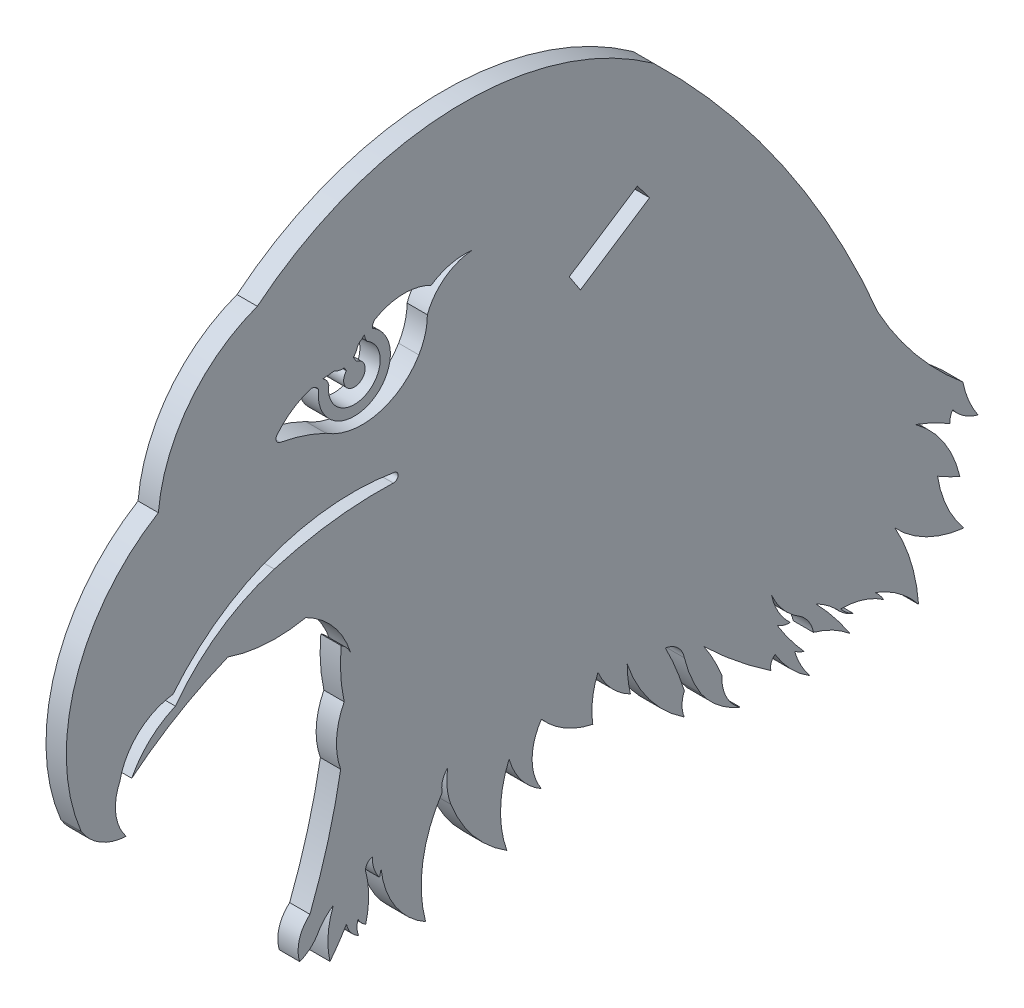
SolidWorks part; units mm, degrees
ref_plane "Front Plane" through (0, 0, 0) normal (0, 0, 1) x (1, 0, 0)
ref_plane "Top Plane" through (0, 0, 0) normal (0, 1, 0) x (1, 0, 0)
ref_plane "Right Plane" through (0, 0, 0) normal (1, 0, 0) x (0, 0, -1)
sketch "Sketch1" plane through (0, 0, 0) normal (1, 0, 0) x (0, 0, -1)
  line L0 (-5.157, -1.535) -> (-5.157, 113.227) construction
  line L1 (-57.5068, 40.0093) -> (-57.736, 40.3716)
  line L2 (-58.2534, 39.7641) -> (-58.4265, 40.0378)
  line L3 (-40.6972, 36.2408) -> (-41.5304, 37.5169)
  line L4 (-41.5304, 37.5169) -> (-36.4188, 40.8543)
  line L6 (-36.4188, 40.8543) -> (-35.4983, 39.6353)
  line L8 (-35.4983, 39.6353) -> (-40.6972, 36.2408)
  arc A102 (-56.508, 41.2313) -> (-59.9592, 39.5319) centre (-57.66, 39.2166) cw construction
  arc A103 (-39.7661, 7.5382) -> (-39.3767, 10.7275) centre (-33.821, 8.4307) cw
  arc A104 (-43.6183, 9.7965) -> (-39.7661, 7.5382) centre (-38.3341, 14.3956) ccw
  arc A105 (-43.6183, 5.2799) -> (-43.6183, 9.7965) centre (-40.3275, 7.5382) cw
  arc A106 (-46.0451, 8.4226) -> (-43.6183, 5.2799) centre (-41.0176, 9.7965) ccw
  arc A107 (-46.2125, 2.5605) -> (-46.0451, 8.4226) centre (-38.7171, 5.2799) cw
  arc A108 (-50.4104, 7.6526) -> (-46.2125, 2.5605) centre (-40.7067, 11.3758) ccw
  arc A109 (-50.6521, 10.1597) -> (-50.4104, 7.6526) centre (-46.0063, 9.3425) ccw
  arc A110 (-51.0669, 8.7672) -> (-50.6521, 10.1597) centre (-49.6143, 9.0925) cw
  arc A111 (-36.9389, 8.0929) -> (-39.3767, 10.7275) centre (-34.4893, 12.8046) cw
  arc A112 (-37.181, 10.1597) -> (-36.9389, 8.0929) centre (-27.6651, 10.2266) ccw
  arc A113 (-32.8896, 4.5676) -> (-37.181, 10.1597) centre (-26.8849, 13.6183) cw
  arc A114 (-32.8896, 6.2719) -> (-32.8896, 4.5676) centre (-30.947, 5.4198) ccw
  arc A115 (-34.3147, 9.774) -> (-32.8896, 6.2719) centre (-53.5231, -0.0839) cw
  arc A116 (-32.8896, 8.4226) -> (-34.3147, 9.774) centre (-34.5555, 8.0929) ccw
  arc A117 (-31.6349, 5.4546) -> (-32.8896, 8.4226) centre (-23.0512, 10.8322) cw
  arc A118 (-28.6904, 3.1113) -> (-31.6349, 5.4546) centre (-26.2232, 9.2331) cw
  arc A119 (-30.0731, 5.8899) -> (-28.6904, 3.1113) centre (-26.941, 5.7151) ccw
  arc A120 (-31.423, 8.4226) -> (-30.0731, 5.8899) centre (-43.6183, 0.2968) cw
  arc A121 (-26.3889, 4.3396) -> (-31.423, 8.4226) centre (-5.4221, 35.3348) cw
  arc A122 (-26.0773, 5.2334) -> (-26.3889, 4.3396) centre (-25.6051, 4.5676) ccw
  arc A123 (-52.3123, 0.9777) -> (-51.0669, 8.7672) centre (-42.9916, 3.4818) cw
  arc A124 (-55.6544, 6.0835) -> (-52.3123, 0.9777) centre (-48.9859, 6.8018) ccw
  arc A125 (-55.763, 5.581) -> (-55.6544, 6.0835) centre (-52.1689, 5.0674) cw
  arc A126 (-56.3189, 7.195) -> (-55.763, 5.581) centre (-53.8194, 7.1531) ccw
  arc A127 (-56.8126, 6.5016) -> (-56.3189, 7.195) centre (-56.1989, 6.5871) cw
  arc A128 (-56.8126, 3.058) -> (-56.8126, 6.5016) centre (-63.2666, 4.7798) ccw
  arc A129 (-57.3883, 3.6721) -> (-56.8126, 3.058) centre (-56.0238, 4.3743) ccw
  arc A130 (-57.3325, 2.5959) -> (-57.3883, 3.6721) centre (-55.9912, 3.2049) cw
  arc A131 (-58.2536, 3.7943) -> (-57.3325, 2.5959) centre (-56.5677, 4.1369) ccw
  arc A132 (-23.4374, 2.5249) -> (-26.0773, 5.2334) centre (-19.2612, 9.236) cw
  arc A133 (-24.6137, 4.703) -> (-23.4374, 2.5249) centre (-18.8822, 6.3917) ccw
  arc A134 (-23.9034, 4.3396) -> (-24.6137, 4.703) centre (-23.0333, 6.9168) cw
  arc A135 (-25.9299, 7.0524) -> (-23.9034, 4.3396) centre (-9.2236, 17.4195) ccw
  arc A136 (-24.9371, 6.7473) -> (-25.9299, 7.0524) centre (-24.9656, 8.4226) cw
  arc A137 (-26.3438, 9.2205) -> (-24.9371, 6.7473) centre (-21.8152, 10.1597) ccw
  arc A138 (-24.1654, 6.7473) -> (-26.3438, 9.2205) centre (-21.4141, 11.3667) cw
  arc A139 (-23.2036, 5.2334) -> (-24.1654, 6.7473) centre (-25.5653, 4.7954) ccw
  arc A140 (-20.4638, 3.7943) -> (-23.2036, 5.2334) centre (-25.2319, -1.9557) ccw
  arc A141 (-23.0216, 6.9921) -> (-20.4638, 3.7943) centre (-38.3705, -7.9066) cw
  arc A142 (-21.4881, 5.8899) -> (-23.0216, 6.9921) centre (-25.7182, 1.6227) ccw
  arc A143 (-20.2087, 4.9703) -> (-21.4881, 5.8899) centre (-19.0523, 7.9289) cw
  arc A144 (-21.1717, 5.7376) -> (-20.2087, 4.9703) centre (-18.895, 7.6071) ccw
  arc A145 (-17.9051, 4.7108) -> (-21.1717, 5.7376) centre (-21.1516, 0.0918) ccw
  arc A146 (-17.9051, 4.7108) -> (-18.5639, 5.5084) centre (-21.4104, 2.4864) ccw
  arc A147 (-15.3111, 3.1113) -> (-18.5639, 5.5084) centre (-21.2448, -1.535) ccw
  arc A148 (-17.0835, 8.9562) -> (-15.3111, 3.1113) centre (-29.2416, 2.0782) cw
  arc A149 (-11.9046, 6.3713) -> (-17.0835, 8.9562) centre (-10.9858, 14.6927) cw
  arc A150 (-13.8837, 10.7275) -> (-11.9046, 6.3713) centre (-5.157, 12.0646) ccw
  arc A151 (-12.2144, 9.8825) -> (-13.8837, 10.7275) centre (-6.9373, 22.3791) cw
  arc A152 (-15.5359, 14.9115) -> (-12.2144, 9.8825) centre (-20.5903, 7.9618) cw
  arc A153 (-59.4908, 1.9849) -> (-58.2536, 3.7943) centre (-71.3915, 11.4489) ccw
  arc A154 (-74.3728, 21.3352) -> (-67.1612, 25.6056) centre (-56.0439, -1.3932) cw
  arc A155 (-71.0947, 24.3852) -> (-74.3728, 21.3352) centre (-68.5194, 18.3306) ccw
  arc A156 (-63.6766, 29.5837) -> (-71.0947, 24.3852) centre (-59.654, 15.9518) ccw
  arc A157 (-54.7401, 30.7082) -> (-63.6766, 29.5837) centre (-55.763, 2.7655) ccw
  arc A158 (-54.6268, 31.3605) -> (-54.7401, 30.7082) centre (-54.7113, 31.0392) cw
  arc A159 (-61.7637, 31.175) -> (-54.6268, 31.3605) centre (-57.7329, 13.481) cw
  arc A160 (-64.9455, 47.3024) -> (-35.2097, 48.2329) centre (-49.4679, 28.2832) cw
  arc A161 (-72.3751, 37.5978) -> (-64.9455, 47.3024) centre (-60.9952, 36.582) cw
  arc A162 (-71.277, 25.2464) -> (-61.7637, 31.175) centre (-57.9587, 14.4723) cw
  arc A163 (-75.2689, 21.5594) -> (-71.277, 25.2464) centre (-70.7065, 20.6242) cw
  arc A164 (-74.7866, 17.7699) -> (-75.2689, 21.5594) centre (-71.9693, 20.0539) cw
  arc A165 (-78.1627, 19.768) -> (-74.7866, 17.7699) centre (-74.5648, 21.996) ccw
  arc A166 (-72.3751, 37.5978) -> (-78.1627, 19.768) centre (-64.9455, 25.3319) ccw
  arc A167 (-56.6971, 40.9005) -> (-59.5818, 39.4802) centre (-57.66, 39.2166) cw
  arc A168 (-56.3189, 41.562) -> (-60.3367, 39.5837) centre (-57.66, 39.2166) cw
  arc A169 (-51.9045, 42.1379) -> (-56.1454, 42.0173) centre (-53.9173, 38.2909) ccw
  arc A170 (-48.8488, 42.8827) -> (-51.9045, 42.1379) centre (-49.4031, 38.5158) ccw
  arc A171 (-52.182, 40.3717) -> (-48.8488, 42.8827) centre (-48.5389, 39.0034) cw
  arc A172 (-52.8158, 38.0759) -> (-52.182, 40.3717) centre (-56.6299, 40.3642) ccw
  arc A173 (-59.1232, 40.1892) -> (-59.5459, 40.1588) centre (-59.2734, 39.3253) ccw
  arc A174 (-57.4831, 40.769) -> (-57.736, 40.3716) centre (-58.5461, 41.1662) cw
  arc A175 (-57.5068, 40.0093) -> (-58.2534, 39.7641) centre (-57.66, 39.2166) cw
  arc A176 (-59.2397, 5.5084) -> (-59.4908, 1.9849) centre (-53.7451, 3.3462) ccw
  arc A177 (-60.4376, 4.2025) -> (-59.2397, 5.5084) centre (-57.298, 2.5249) cw
  arc A178 (-59.8047, 36.4815) -> (-52.8158, 38.0759) centre (-57.0751, 40.6313) ccw
  arc A179 (-63.2284, 37.5978) -> (-59.8047, 36.4815) centre (-65.6968, 24.219) cw
  arc A180 (-61.7637, 3.1113) -> (-60.4376, 4.2025) centre (-62.7225, 5.6279) ccw
  arc A181 (-60.9952, 5.802) -> (-61.7637, 3.1113) centre (-59.3558, 3.8787) ccw
  arc A182 (-12.9372, 13.6727) -> (-15.5359, 14.9115) centre (-21.321, -0.5693) ccw
  arc A183 (-12.7449, 14.4723) -> (-12.9372, 13.6727) centre (-11.888, 13.8433) ccw
  arc A184 (-10.8498, 13.19) -> (-12.7449, 14.4723) centre (-9.9344, 16.5846) cw
  arc A185 (-11.9859, 15.9008) -> (-10.8498, 13.19) centre (-4.7277, 17.3494) ccw
  arc A186 (-18.3627, 23.6272) -> (-11.9859, 15.9008) centre (5.2836, 36.6486) ccw
  arc A187 (-35.2097, 48.2329) -> (-18.3627, 23.6272) centre (-87.0751, -5.3485) cw
  arc A188 (-58.688, 14.0756) -> (-60.9952, 5.802) centre (-102.1357, 21.7334) cw
  arc A189 (-58.4265, 18.3306) -> (-58.688, 14.0756) centre (-53.6384, 15.9008) ccw
  arc A190 (-58.6557, 22.0985) -> (-58.4265, 18.3306) centre (-46.5277, 20.9454) ccw
  arc A191 (-57.9587, 21.3352) -> (-58.6557, 22.0985) centre (-59.6393, 20.5005) ccw
  arc A192 (-60.8769, 39.9443) -> (-63.4563, 38.2111) centre (-59.3884, 34.9431) ccw
  arc A193 (-56.8937, 41.4518) -> (-57.1074, 41.236) centre (-53.9173, 38.2909) ccw
  arc A194 (-60.3367, 39.5837) -> (-60.8769, 39.9443) centre (-60.9668, 39.2247) ccw
  arc A195 (-59.5818, 39.4802) -> (-60.0384, 40.1205) centre (-60.4376, 39.3528) ccw
  arc A196 (-56.3189, 41.562) -> (-56.1454, 42.0173) centre (-55.6912, 41.5835) cw
  arc A197 (-56.6971, 40.9005) -> (-56.8937, 41.4518) centre (-55.9932, 41.4622) cw
  arc A198 (-61.3066, 25.2464) -> (-57.9587, 21.3352) centre (-64.3017, 19.2941) cw
  arc A199 (-67.1612, 25.6056) -> (-61.3066, 25.2464) centre (-63.5764, 36.1424) ccw
  arc A200 (-59.5459, 40.1588) -> (-60.0384, 40.1205) centre (-59.3884, 34.9431) ccw
  arc A201 (-63.4563, 38.2111) -> (-63.2284, 37.5978) centre (-63.1593, 37.9725) ccw
  arc A202 (-58.4265, 40.0378) -> (-59.1232, 40.1892) centre (-58.5461, 41.1662) cw
  arc A203 (-57.1074, 41.236) -> (-57.4831, 40.769) centre (-56.8126, 40.6142) ccw
extrude "Boss-Extrude1" add sketch "Sketch1" along normal blind 1.524
